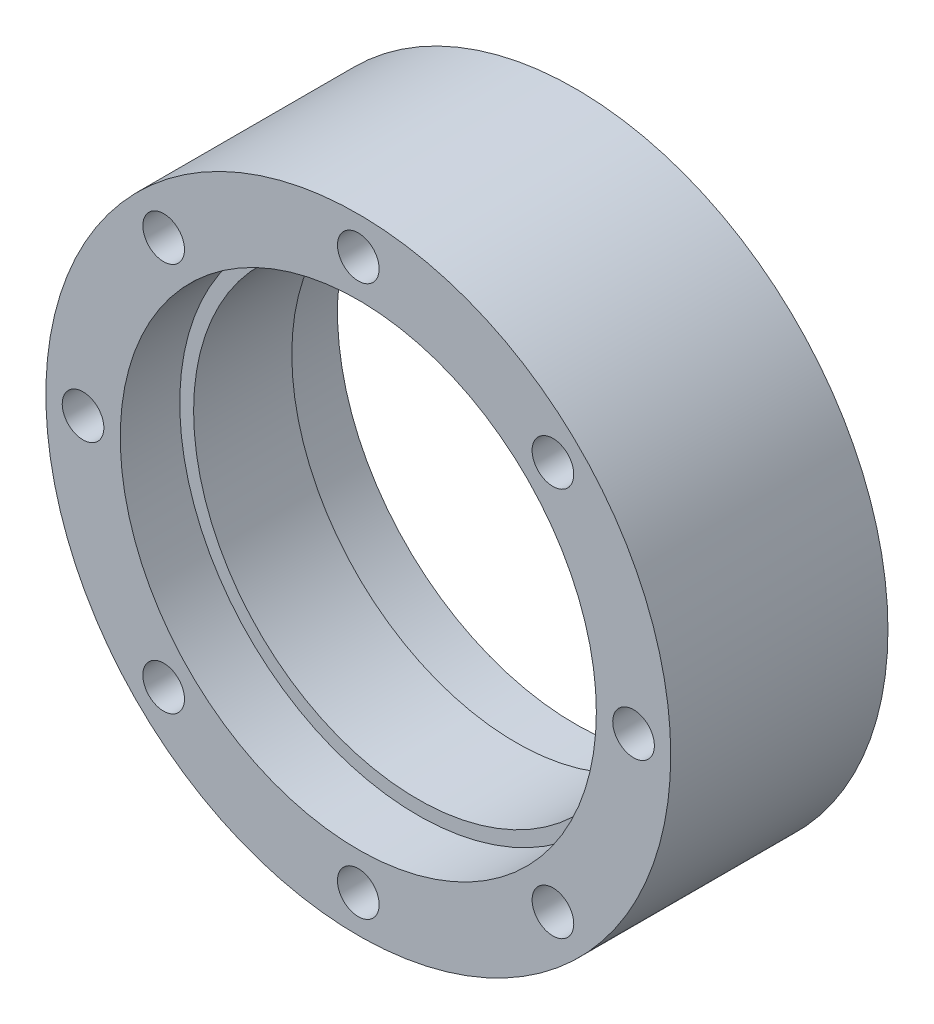
SolidWorks part; units mm, degrees
ref_plane "Front Plane" through (0, 0, 0) normal (0, 0, 1) x (1, 0, 0)
ref_plane "Top Plane" through (0, 0, 0) normal (0, 1, 0) x (1, 0, 0)
ref_plane "Right Plane" through (0, 0, 0) normal (1, 0, 0) x (0, 0, -1)
ref_axis "Z" through (0, 0, 8.03) along (0, 0, -1)
sketch "Sketch7" plane through (0, 0, 0) normal (0, 1, 0) x (1, 0, 0)
  line L0 (16, 7.3) -> (16, 3.3)
  line L2 (16, 3.3) -> (15.07, 3.3)
  line L5 (16, 7.3) -> (21, 7.3)
  line L6 (21, 7.3) -> (21, -7.3)
  line L7 (24.7452, 0) -> (-6.4078, 0) construction
  line L8 (16, -3.3) -> (15.07, -3.3)
  line L9 (16, -7.3) -> (16, -3.3)
  line L10 (15.07, 3.3) -> (15.07, -3.3)
  line L11 (21, -7.3) -> (16, -7.3)
  line L12 (0, -8.03) -> (0, 8.03) construction
  dimension "D2" = 4
  dimension "D4" = 3.3
  dimension "D1" = 15.07
  dimension "D3" = 16
  dimension "D5" = 21
revolve "Revolve1" add sketch "Sketch7" angle 360 about axis through (0, 0, 8.03) along (0, 0, -1)
sketch "Sketch3" plane through (0, 0, 0) normal (0, 0, 1) x (1, 0, 0)
  line L0 (0, 0) -> (0, 18.5) construction
  circle A0 centre (0, 18.5) radius 1.4
  dimension "D1" = 2.8
  dimension "D2" = 18.5
extrude "Cut-Extrude2" cut sketch "Sketch3" against normal through all both and the other way through all
sketch "Sketch4" plane through (0, 0, -7.3) normal (0, 0, -1) x (-1, 0, 0)
  circle A0 centre (0, 18.5) radius 2.35
  circle A1 centre (0, 18.5) radius 1.4 construction
  dimension "D1" = 4.7
extrude "Cut-Extrude4" cut sketch "Sketch4" against normal blind 2.5 and the other way through all
chamfer "Chamfer1" distance 0.1 angle 45 1 edges at (-1.4, 18.5, -4.8)
pattern_circular "CirPattern3" count 4 over 360 about axis through (0, 0, 0) along (0, 0, 1) of "Cut-Extrude4"
pattern_circular "CirPattern2" count 8 over 360 about axis through (0, 0, 0) along (0, 0, 1) of "Cut-Extrude2"
equation "\"BearingOD\"= 32"
equation "\"BearingHeight\"= 4"
equation "\"SeatsOD\"= \"BearingOD\" + 10"
equation "\"RetainingRingThickness\" = 1.30"
equation "\"BearingBaseDistance\"= 17.2 - 2*\"BearingHeight\"  - \"RetainingRingThickness\"*2"
equation "\"WireHarnessHeight\"= 4"
equation "\"OuterWallWidth\"= 6"
equation "\"OverallOD\" = 42"
equation "\"BearingID\" = 25"
equation "\"OverallHeight\"= \"WireHarnessHeight\" + \"BearingHeight\"*2 + \"BearingBaseDistance\""
equation "\"RetaininRingGrooveDiameter\" = 23.9"
equation "\"ShaftLengthAfterFlange\" = 2*\"BearingHeight\" + \"BearingBaseDistance\" + \"RetainingRingThickness\"*2\t'give a retaining ring thickness of extra clearance"
equation "\"RetainingRingGrooveBase\" = \"ShaftLengthAfterFlange\" - \"RetainingRingThickness\"*2"
equation "\"CoverThickness\" = 1"
equation "\"CoverClearance\" = 1"
equation "\"FlangHeight\" = 3"
equation "\"OuterHousingHeight\" = \"WireHarnessHeight\" + \"BearingHeight\"*2 + \"BearingBaseDistance\""
equation "\"PCBWidth\" = 5"
equation "\"PCBHeight\" = \"OuterHousingHeight\" "
equation "\"PCBThickness\" = 1"
equation "\"NormalDistSidewallPCBToZ\" = (\"OverallOD\"/2) - 1.6\t'radial distance from the z axis to pcb origin on the top/connector side"
equation "\"PCBSidewallCutoutClearance\"= 0.1"
equation "\"D3@Sketch7\"=\"BearingOD\"/2"
equation "\"D4@Sketch7\"=\"BearingBaseDistance\"/2"
equation "\"D5@Sketch7\"=\"OverallOD\"/2"
equation "\"D2@Sketch3\"=(\"OverallOD\"+\"BearingOD\")/4"
equation "\"OutputHubBoltCircleRadius\"= 8"
equation "\"OutputHubOD\"= 27"
equation "\"BearingInnerRaceOD\"= 26.9"
equation "\"StatorWireRadius\"= \"NormalDistSidewallPCBToZ\" - 5.7"
equation "\"MountingHoleRadius\"= (\"OverallOD\"+\"BearingOD\")/4"
